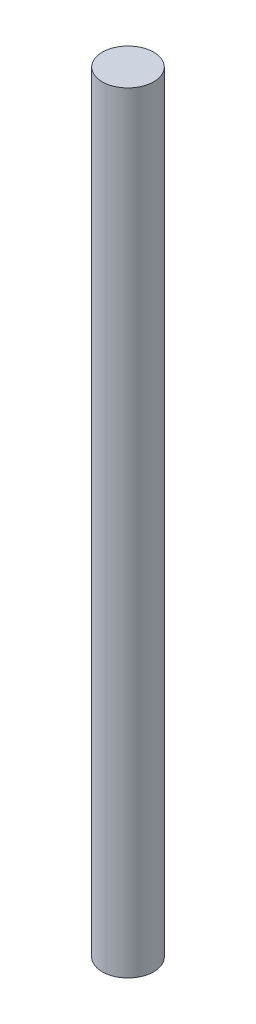
SolidWorks part; units mm, degrees
ref_plane "Front Plane" through (0, 0, 0) normal (0, 0, 1) x (1, 0, 0)
ref_plane "Top Plane" through (0, 0, 0) normal (0, 1, 0) x (1, 0, 0)
ref_plane "Right Plane" through (0, 0, 0) normal (1, 0, 0) x (0, 0, -1)
sketch "Sketch1" plane through (0, 0, 0) normal (0, 1, 0) x (1, 0, 0)
  circle A0 centre (0, 0) radius 7.5
  dimension "D1" = 15
extrude "Boss-Extrude1" add sketch "Sketch1" along normal blind 225
